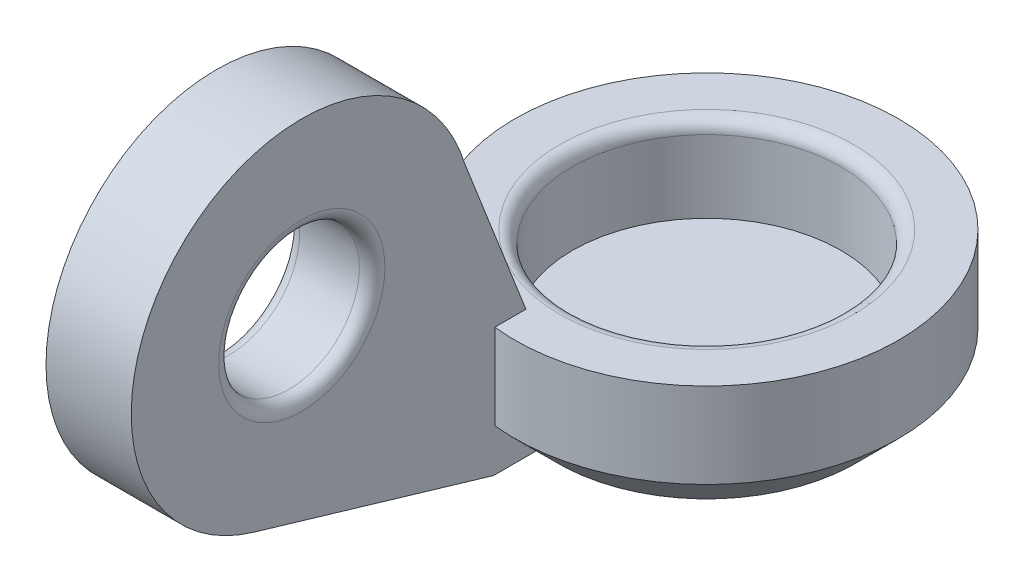
SolidWorks part; units mm, degrees
ref_plane "前视基准面" through (0, 0, 0) normal (0, 0, 1) x (1, 0, 0)
ref_plane "上视基准面" through (0, 0, 0) normal (0, 1, 0) x (1, 0, 0)
ref_plane "右视基准面" through (0, 0, 0) normal (1, 0, 0) x (0, 0, -1)
ref_plane "基准面4" through (0, 0, 5) normal (0, 0, 1) x (1, 0, 0)
sketch "草图6" plane through (0, 0, 0) normal (0, 1, 0) x (1, 0, 0)
  circle A1 centre (0, 0) radius 4.5
  dimension "D2" = 9
extrude "凸台-拉伸4" add sketch "草图6" against normal blind 3
sketch "草图7" plane through (0, 0, 0) normal (0, 1, 0) x (1, 0, 0)
  circle A0 centre (0, 0) radius 3.15
  dimension "D1" = 6.3
extrude "切除-拉伸4" cut sketch "草图7" against normal blind 2
sketch "草图15" plane through (0, 0, 0) normal (1, 0, 0) x (0, 0, -1)
  line L0 (4.5, -3) -> (4.5, -2)
  line L1 (4.5, -3) -> (4.5, 0) construction
  line L2 (4.5, -2) -> (3.5, -3)
  line L3 (-4.5, -3) -> (4.5, -3) construction
  line L4 (3.5, -3) -> (4.5, -3)
  line L5 (0, 0) -> (0, -5.1647) construction
  dimension "D1" = 1
  dimension "D2" = 1
revolve "切除-旋转2" cut sketch "草图15" angle 360 about L5
ref_plane "基准面11" through (-0.5, 0, 0) normal (1, 0, 0) x (0, 0, -1)
sketch "草图8" plane through (-0.5, 0, 0) normal (1, 0, 0) x (0, 0, -1)
  line L0 (0, -3) -> (0, 6.4628) construction
  line L1 (-4.5, -3) -> (4.5, -3) construction
  line L2 (4.5, 0) -> (-4.5, 0) construction
  circle A0 centre (-9, 2.5) radius 4
  dimension "D2" = 8
  dimension "D1" = 9
  dimension "D3" = 2.5
extrude "凸台-拉伸5" add sketch "草图8" against normal blind 2 separate body
sketch "草图9" plane through (-0.5, 0, 0) normal (1, 0, 0) x (0, 0, -1)
  line L1 (4.5, 0) -> (-4.5, 0) construction
  line L2 (-4.5, -3) -> (-10.1331, -1.3362)
  line L3 (-9, 2.5) -> (-10.1331, -1.3362) construction
  line L4 (-9, 2.5) -> (-5.1529, 3.6956) construction
  line L8 (-5.1529, 3.6956) -> (-10.1331, -1.3362)
  line L10 (-4.5, -3) -> (4.5, -3) construction
  line L11 (-3.529, -3) -> (-4.5, -3)
  line L12 (-5.1529, 3.6956) -> (-3.5, 0)
  line L13 (-3.5, 0) -> (-3.5, -3)
  line L14 (-3.5, -3) -> (-3.529, -3)
  circle A0 centre (-9, 2.5) radius 4 construction
  dimension "D1" = 3.5
extrude "凸台-拉伸7" add sketch "草图9" against normal up to surface (2 mm away) up to face at (-2.5, 2.5, 5)
sketch "草图16" plane through (0, 0, 3.5) normal (0, 0, -1) x (-1, 0, 0)
  line L0 (2.5, -3) -> (2.5, -2.1988)
  line L1 (2.5, -2.1988) -> (0.5, -2.9557)
  line L2 (0.5, -2.9557) -> (0.5, -3)
  line L3 (0.5, -3) -> (2.5, -3)
extrude "凸台-拉伸8" add sketch "草图16" along normal up to next
sketch "草图11" plane through (-0.5, 0, 0) normal (1, 0, 0) x (0, 0, -1)
  circle A0 centre (-9, 2.5) radius 1.65
  dimension "D1" = 3.3
extrude "切除-拉伸6" cut sketch "草图11" against normal blind 2
sketch "草图12" plane through (-2.5, 0, 0) normal (-1, 0, 0) x (0, 0, 1)
  line L0 (3.5, 0) -> (3.7417, 0)
  line L2 (5.1529, 3.6956) -> (3.5, 0)
  line L3 (5.1529, 3.6956) -> (5.1757, 3.6726)
  line L4 (5.1757, 3.6726) -> (3.7417, 0)
extrude "切除-拉伸7" cut sketch "草图12" against normal up to next
fillet "圆角1" radius 0.3 1 edges at (0, 0, 3.15)
fillet "圆角2" radius 0.3 1 edges at (-0.5, 2.5, 7.35)
ref_plane "基准面13" through (0, 0, 9) normal (0, 0, 1) x (1, 0, 0)
sketch "草图14" plane through (0, 0, 9) normal (0, 0, 1) x (1, 0, 0)
  line L0 (-6.6956, 2.5) -> (6.2787, 2.5) construction
  line L1 (-0.5, 6.5) -> (-2.5, 6.5) construction
  line L2 (-2.8, 2.5) -> (-2.5, 2.5)
  line L4 (-2.5, 2.5) -> (-2.5, 6.5)
  arc A0 (-2.5, 6.5) -> (-2.8, 2.5) centre (34.8421, 1.6881) ccw
  dimension "D1" = 4
  dimension "D2" = 0.3
revolve "旋转3" [suppressed] add sketch "草图14" angle 360 about L0
fillet "圆角3" radius 0.3 1 edges at (-2.5, 2.5, 7.35)
